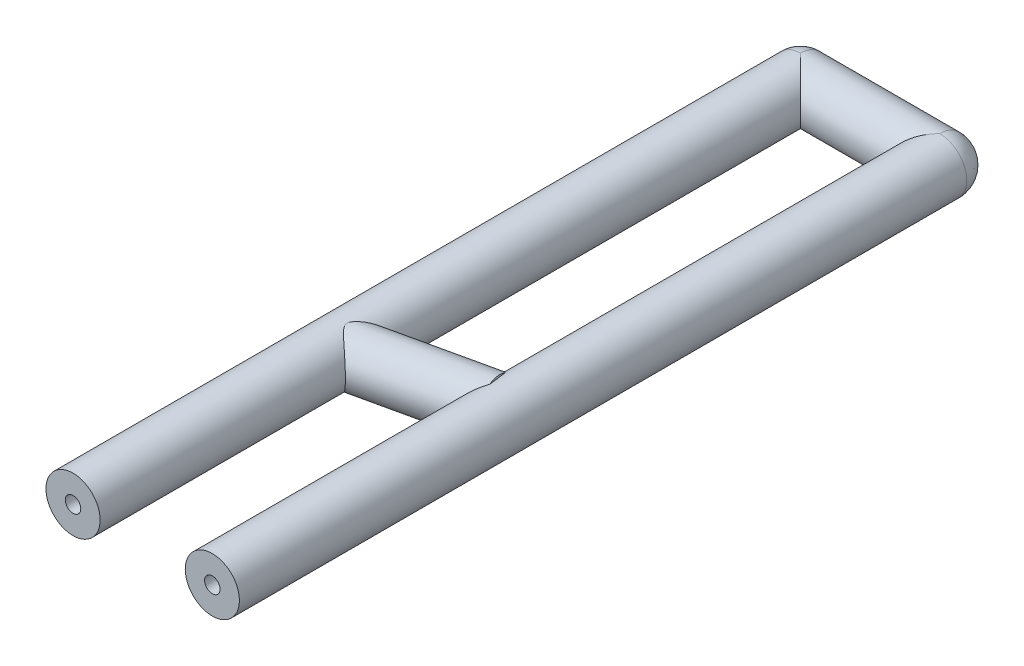
SolidWorks part; units mm, degrees
ref_plane "前基準面" through (0, 0, 0) normal (0, 0, 1) x (1, 0, 0)
ref_plane "上基準面" through (0, 0, 0) normal (0, 1, 0) x (1, 0, 0)
ref_plane "右基準面" through (0, 0, 0) normal (1, 0, 0) x (0, 0, -1)
sketch "草圖1" plane through (0, 0, 0) normal (0, 1, 0) x (1, 0, 0)
  line L2 (-4.5, -47) -> (-4.5, 0) construction
  line L3 (-4.5, 0) -> (4.5, 0) construction
  line L4 (4.5, 0) -> (4.5, -47) construction
  line L5 (-2.75, -47) -> (-2.75, -1.75)
  line L6 (-2.75, -1.75) -> (2.75, -1.75)
  line L7 (2.75, -1.75) -> (2.75, -47)
  line L8 (-6.25, -47) -> (-6.25, 1.75)
  line L9 (-6.25, 1.75) -> (6.25, 1.75)
  line L10 (6.25, 1.75) -> (6.25, -47)
  line L11 (-2.75, -47) -> (-6.25, -47)
  line L12 (2.75, -47) -> (6.25, -47)
  line L13 (-4.1, -47) -> (-4.1, -0.4)
  line L14 (-4.1, -0.4) -> (4.1, -0.4)
  line L15 (4.1, -0.4) -> (4.1, -47)
  line L16 (-4.9, -47) -> (-4.9, 0.4)
  line L17 (-4.9, 0.4) -> (4.9, 0.4)
  line L18 (4.9, 0.4) -> (4.9, -47)
  line L19 (-4.1, -47) -> (-4.9, -47)
  line L20 (4.1, -47) -> (4.9, -47)
  line L21 (-4.5, -29.8) -> (4.5, -27.8) construction
  line L22 (-4.1312, -31.4595) -> (4.8688, -29.4595)
  line L23 (-4.8688, -28.1405) -> (4.1312, -26.1405)
  dimension "D6" = 0.4
  dimension "D1" = 47
  dimension "D2" = 47
  dimension "D3" = 9
  dimension "D4" = 1.75
  dimension "D5" = 1.75
  dimension "D7" = 0.4
  dimension "D8" = 29.8
  dimension "D9" = 27.8
  dimension "D10" = 1.7
  dimension "D11" = 1.7
sketch "草圖5" plane through (0, 0, 0) normal (0, 1, 0) x (1, 0, 0)
  line L0 (-4.5, -47) -> (-4.5, 0)
  line L2 (-4.5, 0) -> (4.5, 0) construction
  line L3 (-6.25, -47) -> (-6.25, 1.75) construction
  line L4 (-6.25, 0) -> (-6.25, -47)
  line L5 (-6.25, -47) -> (-2.75, -47)
  line L6 (-2.75, 0) -> (-2.75, -47)
  line L7 (-6.25, 0) -> (-2.75, 0)
revolve "left" add sketch "草圖5" angle 360 about L2
sketch "草圖6" plane through (0, 0, 0) normal (0, 1, 0) x (1, 0, 0)
  line L0 (4.5, -47) -> (4.5, 0)
  line L2 (-4.5, 0) -> (4.5, 0) construction
  line L3 (6.25, 1.75) -> (6.25, -47) construction
  line L4 (6.25, 0) -> (6.25, -47)
  line L5 (6.25, -47) -> (2.75, -47)
  line L6 (2.75, 0) -> (2.75, -47)
  line L7 (2.75, 0) -> (6.25, 0)
revolve "right" add sketch "草圖6" angle 360 about L4
sketch "草圖7" plane through (0, 0, 0) normal (0, 1, 0) x (1, 0, 0)
  line L0 (-4.5, 0) -> (4.5, 0)
  line L3 (-4.5, -47) -> (-4.5, 0) construction
  line L4 (-4.5, 1.75) -> (4.5, 1.75)
  line L5 (-6.25, 1.75) -> (6.25, 1.75) construction
  line L6 (-4.5, -1.75) -> (4.5, -1.75)
  line L7 (4.5, 0) -> (4.5, -47) construction
  line L8 (-4.5, 0) -> (4.5, 0) construction
  line L9 (-4.5, -1.75) -> (-4.5, 1.75)
  line L10 (4.5, -1.75) -> (4.5, 1.75)
  dimension "D1" = 1.75
revolve "down" add sketch "草圖7" angle 360 about L3
sketch "草圖8" plane through (0, 0, 0) normal (0, 0, -1) x (-1, 0, 0)
  line L0 (4.5, -1.75) -> (4.5, 1.75)
  line L1 (4.5, 1.75) -> (4.5, -1.75) construction
  arc A0 (4.5, -1.75) -> (4.5, 1.75) centre (4.5, 0) ccw
revolve "left_orner" add sketch "草圖8" angle 90 about L0
sketch "草圖9" plane through (0, 0, 0) normal (0, 0, -1) x (-1, 0, 0)
  line L0 (-4.5, -1.75) -> (-4.5, 1.75)
  line L1 (-4.5, 1.75) -> (-4.5, -1.75) construction
  arc A0 (-4.5, 1.75) -> (-4.5, -1.75) centre (-4.5, 0) ccw construction
  arc A1 (-4.5, 1.75) -> (-4.5, -1.75) centre (-4.5, 0) ccw
revolve "right_corner" add sketch "草圖9" angle 90 about L0
sketch "草圖10" plane through (0, 0, 0) normal (0, 1, 0) x (1, 0, 0)
  line L0 (-4.1312, -31.4595) -> (-4.1312, -27.9766)
  line L1 (-4.1312, -27.9766) -> (4.1312, -26.1405)
  line L2 (4.1312, -26.1405) -> (4.1312, -29.6234)
  line L3 (4.1312, -29.6234) -> (-4.1312, -31.4595)
  line L4 (-4.1312, -29.718) -> (4.1312, -27.882)
  line L5 (-4.1312, -31.4595) -> (4.8688, -29.4595) construction
  line L6 (-4.8688, -28.1405) -> (4.1312, -26.1405) construction
revolve "up" add sketch "草圖10" angle 360 about L21
sketch "草圖11" plane through (0, 0, 47) normal (0, 0, 1) x (1, 0, 0)
  circle A0 centre (-4.5, 0) radius 0.5
  dimension "D1" = 1
sketch "草圖12" plane through (0, 0, 0) normal (0, 1, 0) x (1, 0, 0)
  line L0 (-4.5, -47) -> (-4.5, -1)
  line L1 (-3.5, 0) -> (3.5, 0)
  line L2 (4.5, -1) -> (4.5, -47)
  arc A0 (3.5, 0) -> (4.5, -1) centre (3.5, -1) cw
  arc A1 (-4.5, -1) -> (-3.5, 0) centre (-3.5, -1) cw
  point P10 (4.5, 0)
  point P13 (-4.5, 0)
  dimension "D1" = 1
sweep "inside" cut profiles "草圖11" path "草圖12"
ref_plane "平面4" through (4.5, 0, 0) normal (1, 0, 0) x (0, 0, -1)
sketch "草圖13" plane through (4.5, 0, 0) normal (1, 0, 0) x (0, 0, -1)
  circle A0 centre (-27.8, 0) radius 0.5
  dimension "D1" = 1
sketch "草圖14" plane through (0, 0, 0) normal (0, 1, 0) x (1, 0, 0)
  line L0 (4.5, -27.8) -> (-4.5, -29.8)
sweep "up_inside" cut profiles "草圖13" path "草圖14"
ref_plane "平面5" through (0, 0, 38) normal (0, 0, 1) x (1, 0, 0)
sketch "草圖15" plane through (0, 0, 38) normal (0, 0, 1) x (1, 0, 0)
  circle A0 centre (-4.5, 0) radius 0.4
  circle A1 centre (-4.5, 0) radius 0.5 construction
  dimension "D1" = 0.8
sketch "草圖16" plane through (0, 0, 0) normal (0, 1, 0) x (1, 0, 0)
  line L0 (-4.5, -38) -> (-4.5, -1)
  line L1 (-3.5, 0) -> (3.5, 0)
  line L2 (4.5, -1) -> (4.5, -38)
  arc A0 (3.5, 0) -> (4.5, -1) centre (3.5, -1) cw
  arc A1 (-4.5, -1) -> (-3.5, 0) centre (-3.5, -1) cw
  point P9 (4.5, 0)
  point P12 (-4.5, 0)
  dimension "D1" = 1
sweep "掃出6" [suppressed] add profiles "草圖15" path "草圖16"
sketch "草圖17" plane through (4.5, 0, 0) normal (1, 0, 0) x (0, 0, -1)
  circle A0 centre (-27.8, 0) radius 0.4
  dimension "D1" = 0.8
sketch "草圖18" plane through (0, 0, 0) normal (0, 1, 0) x (1, 0, 0)
  line L0 (4.5, -27.8) -> (-4.5, -29.8)
sweep "掃出7" [suppressed] add profiles "草圖17" path "草圖18"
